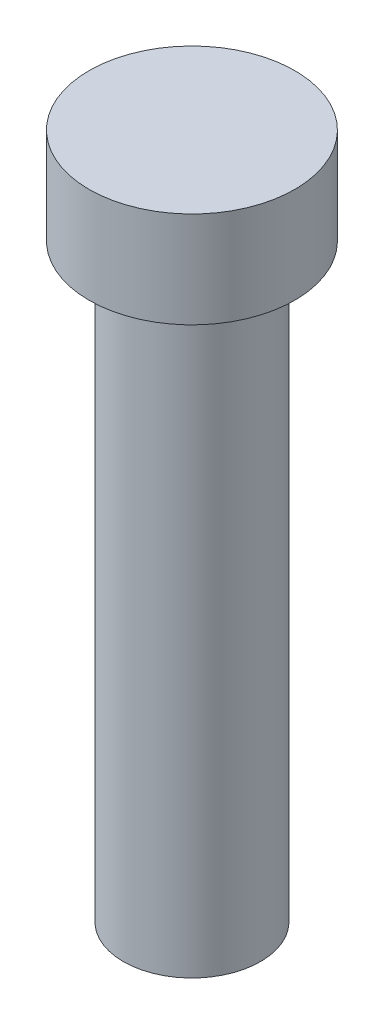
SolidWorks part; units mm, degrees
ref_plane "Front Plane" through (0, 0, 0) normal (0, 0, 1) x (1, 0, 0)
ref_plane "Top Plane" through (0, 0, 0) normal (0, 1, 0) x (1, 0, 0)
ref_plane "Right Plane" through (0, 0, 0) normal (1, 0, 0) x (0, 0, -1)
sketch "Sketch1" plane through (0, 0, 0) normal (0, 1, 0) x (1, 0, 0)
  circle A0 centre (0, 0) radius 5
  dimension "D1" = 10
extrude "Boss-Extrude1" add sketch "Sketch1" along normal blind 43 contours A0
sketch "Sketch2" plane through (0, 43, 0) normal (0, 1, 0) x (1, 0, 0)
  circle A0 centre (0, 0) radius 7.5
  dimension "D1" = 15
extrude "Boss-Extrude2" add sketch "Sketch2" along normal blind 7
